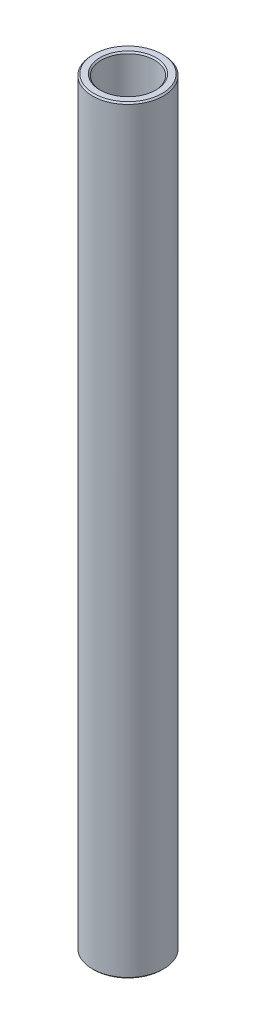
SolidWorks part; units mm, degrees
ref_plane "Front Plane" through (0, 0, 0) normal (0, 0, 1) x (1, 0, 0)
ref_plane "Top Plane" through (0, 0, 0) normal (0, 1, 0) x (1, 0, 0)
ref_plane "Right Plane" through (0, 0, 0) normal (1, 0, 0) x (0, 0, -1)
sketch "Sketch1" plane through (0, 0, 0) normal (0, 0, 1) x (1, 0, 0)
  line L0 (0, 11.6086) -> (0, -11.6086) construction
  line L1 (4.7625, 67.8583) -> (6.35, 67.8583)
  line L2 (6.35, 67.8583) -> (6.35, -67.8583)
  line L3 (6.35, -67.8583) -> (4.7625, -67.8583)
  line L4 (4.7625, -67.8583) -> (4.7625, 67.8583)
  line L5 (4.7625, 0) -> (0, 0) construction
  dimension "D1" = 9.525
  dimension "D2" = 12.7
  dimension "D3" = 135.7166
revolve "Revolve1" add sketch "Sketch1" angle 360 about L0
chamfer "Chamfer1" distance 0.254 angle 45 4 edges at (-4.7625, -67.8583, 0) (-6.35, -67.8583, 0) (-6.35, 67.8583, 0) (-4.7625, 67.8583, 0)
